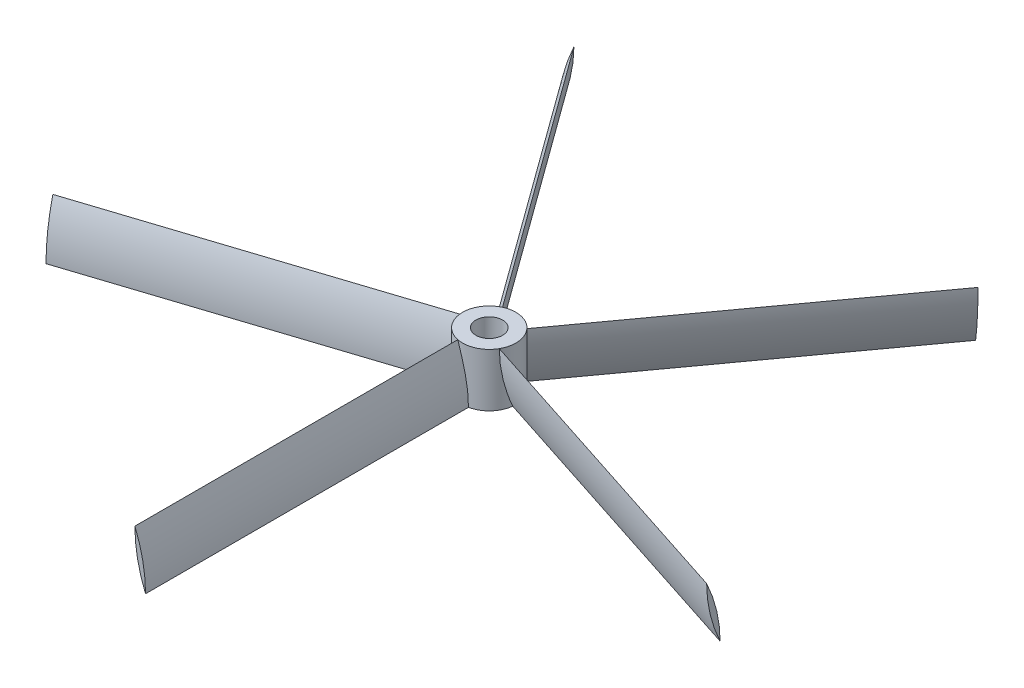
SolidWorks part; units mm, degrees
ref_plane "前视基准面" through (0, 0, 0) normal (0, 0, 1) x (1, 0, 0)
ref_plane "上视基准面" through (0, 0, 0) normal (0, 1, 0) x (1, 0, 0)
ref_plane "右视基准面" through (0, 0, 0) normal (1, 0, 0) x (0, 0, -1)
sketch "草图1" plane through (0, 0, 0) normal (0, 1, 0) x (1, 0, 0)
  circle A0 centre (0, 0) radius 2.5
  circle A1 centre (0, 0) radius 5
  dimension "D1" = 5
  dimension "D2" = 10
extrude "凸台-拉伸1" add sketch "草图1" along normal blind 10
sketch "草图2" plane through (0, 0, 0) normal (0, 0, 1) x (1, 0, 0)
  line L0 (0, 10) -> (0, 0) construction
  line L1 (5, 10) -> (-5, 10) construction
  line L4 (-5, 0) -> (5, 0) construction
  line L5 (-1, 10) -> (1, 0) construction
  arc A0 (-1, 10) -> (1, 0) centre (25, 10) ccw
  arc A1 (-1, 10) -> (1, 0) centre (-25, 0) cw
  dimension "D1" = 1
  dimension "D2" = 1
extrude "凸台-拉伸2" add sketch "草图2" along normal blind 61.5 from offset 4
pattern_circular "阵列(圆周)1" count 5 every 72 about axis through (0, 0, 0) along (0, 1, 0) of "凸台-拉伸2"
